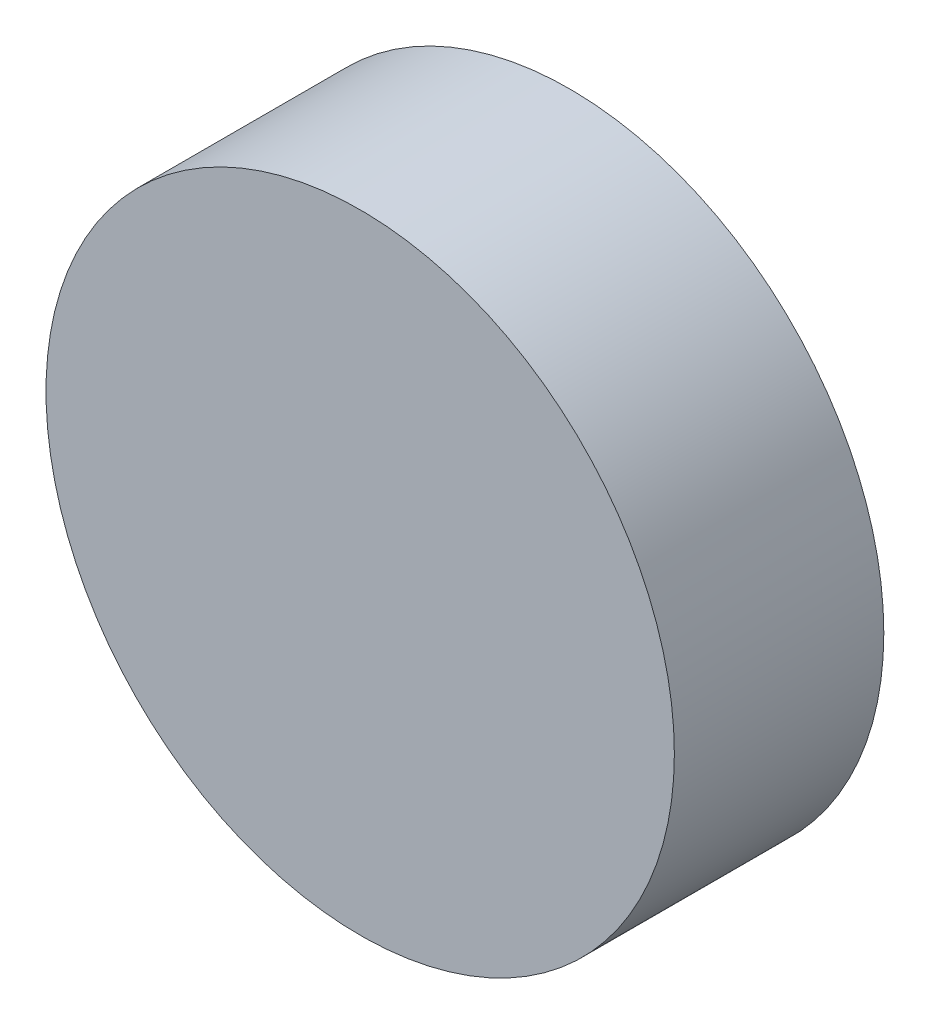
SolidWorks part; units mm, degrees
ref_plane "Front Plane" through (0, 0, 0) normal (0, 0, 1) x (1, 0, 0)
ref_plane "Top Plane" through (0, 0, 0) normal (0, 1, 0) x (1, 0, 0)
ref_plane "Right Plane" through (0, 0, 0) normal (1, 0, 0) x (0, 0, -1)
sketch "Sketch1" plane through (0, 0, 0) normal (0, 0, 1) x (1, 0, 0)
  circle A0 centre (0, 0) radius 2.3813
  dimension "D1" = 4.7625
extrude "Boss-Extrude1" add sketch "Sketch1" along normal blind 1.5875
